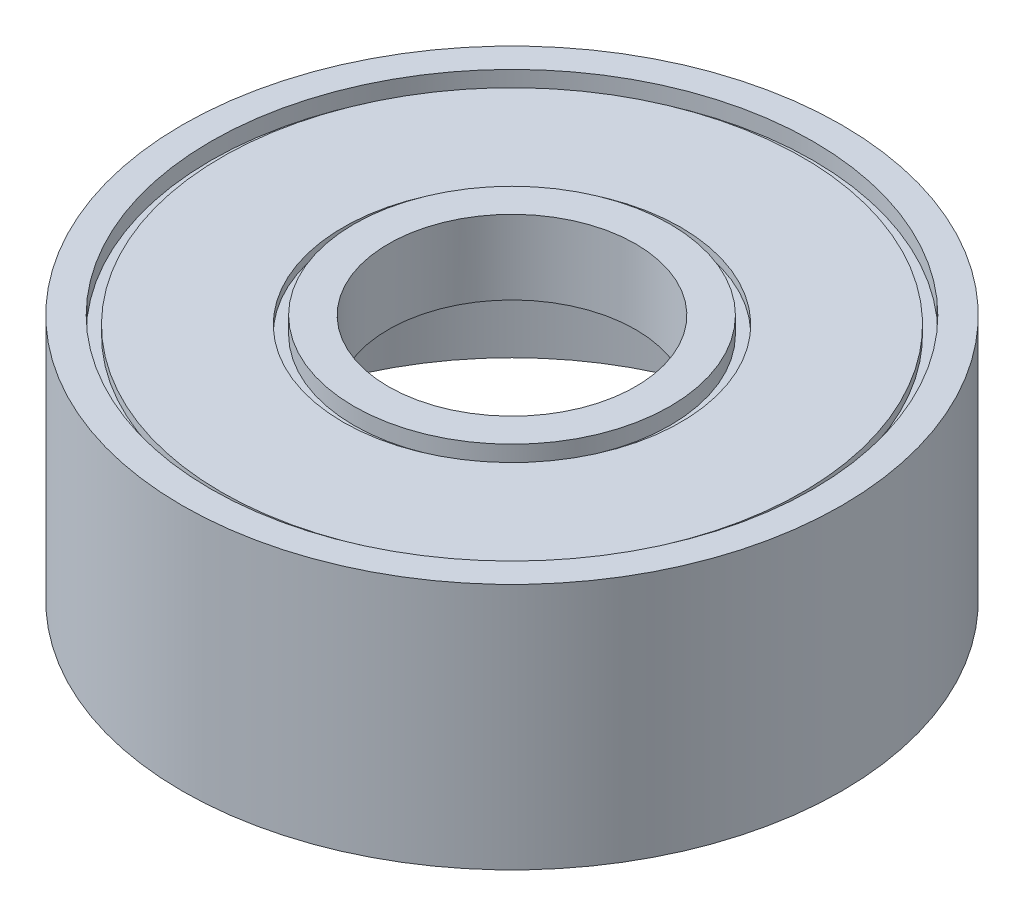
SolidWorks part; units mm, degrees
material "AISI 1020 Steel, Cold Rolled"
ref_plane "Front Plane" through (0, 0, 0) normal (0, 0, 1) x (1, 0, 0)
ref_plane "Top Plane" through (0, 0, 0) normal (0, 1, 0) x (1, 0, 0)
ref_plane "Right Plane" through (0, 0, 0) normal (1, 0, 0) x (0, 0, -1)
sketch "Sketch1" plane through (0, 0, 0) normal (0, 1, 0) x (1, 0, 0)
  circle A0 centre (0, 0) radius 1.5
  circle A1 centre (0, 0) radius 4
extrude "Boss-Extrude1" add sketch "Sketch1" along normal blind 3
sketch "Sketch2" plane through (0, 3, 0) normal (0, 1, 0) x (1, 0, 0)
  circle A0 centre (0, 0) radius 1.9167
  circle A1 centre (0, 0) radius 3.6532
extrude "Cut-Extrude1" cut sketch "Sketch2" against normal blind 0.1
sketch "Sketch4" plane through (0, 2.9, 0) normal (0, 1, 0) x (1, 0, 0)
  circle A0 centre (0, 0) radius 1.9167
  circle A1 centre (0, 0) radius 2.0481
extrude "Cut-Extrude6" cut sketch "Sketch4" against normal blind 0.1
sketch "Sketch5" plane through (0, 2.9, 0) normal (0, 1, 0) x (1, 0, 0)
  circle A0 centre (0, 0) radius 3.6532
  circle A1 centre (0, 0) radius 3.5221
extrude "Cut-Extrude7" cut sketch "Sketch5" against normal blind 0.1
sketch "Sketch6" plane through (0, 0, 0) normal (0, -1, 0) x (1, 0, 0)
  circle A0 centre (0, 0) radius 3.6112
extrude "Cut-Extrude8" cut sketch "Sketch6" against normal blind 2.1
